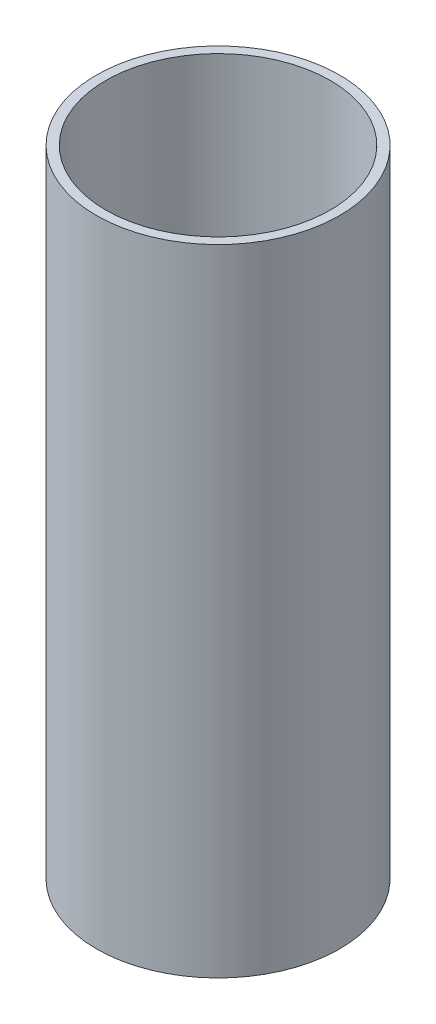
SolidWorks part; units mm, degrees
material "Acrylic (Medium-high impact)"
ref_plane "Front Plane" through (0, 0, 0) normal (0, 0, 1) x (1, 0, 0)
ref_plane "Top Plane" through (0, 0, 0) normal (0, 1, 0) x (1, 0, 0)
ref_plane "Right Plane" through (0, 0, 0) normal (1, 0, 0) x (0, 0, -1)
sketch "Sketch1" plane through (0, 0, 0) normal (0, 1, 0) x (1, 0, 0)
  circle A0 centre (0, 0) radius 76.2
  circle A1 centre (0, 0) radius 82.55
  dimension "D1" = 152.4
  dimension "D2" = 6.35
extrude "Boss-Extrude1" add sketch "Sketch1" along normal mid plane 431
